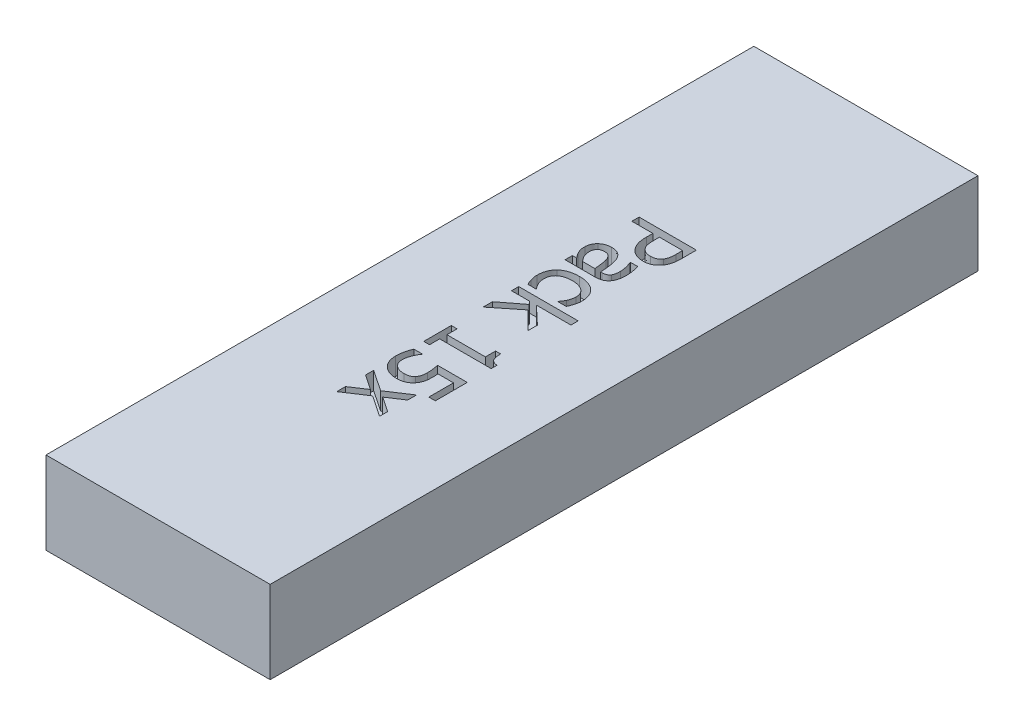
SolidWorks part; units mm, degrees
material "Rubber"
ref_plane "Спереди" through (0, 0, 0) normal (0, 0, 1) x (1, 0, 0)
ref_plane "Сверху" through (0, 0, 0) normal (0, 1, 0) x (1, 0, 0)
ref_plane "Справа" through (0, 0, 0) normal (1, 0, 0) x (0, 0, -1)
sketch "Sketch1" plane through (0, 0, 0) normal (0, 0, 1) x (1, 0, 0)
  line L1 (-19, -7) -> (19, -7)
  line L2 (-19, -7) -> (-19, 7)
  line L3 (-19, 7) -> (19, 7)
  line L4 (19, -7) -> (19, 7)
  line L5 (-19, -7) -> (19, 7) construction
  line L6 (-19, 7) -> (19, -7) construction
  point P0 (0, 0)
  dimension "D1" = 38
  dimension "D2" = 14
extrude "Boss-Extrude1" add sketch "Sketch1" along normal blind 120
sketch "Sketch2" plane through (0, 7, 0) normal (0, 1, 0) x (1, 0, 0)
  line L0 (-3.6534, 0) -> (-3.6534, -120) construction
  line L1 (19, 0) -> (-19, 0) construction
  line L2 (19, -120) -> (-19, -120) construction
  text T0 "Pack 15x" font "Tahoma" height in points 36
extrude "Cut-Extrude1" cut sketch "Sketch2" against normal blind 3
